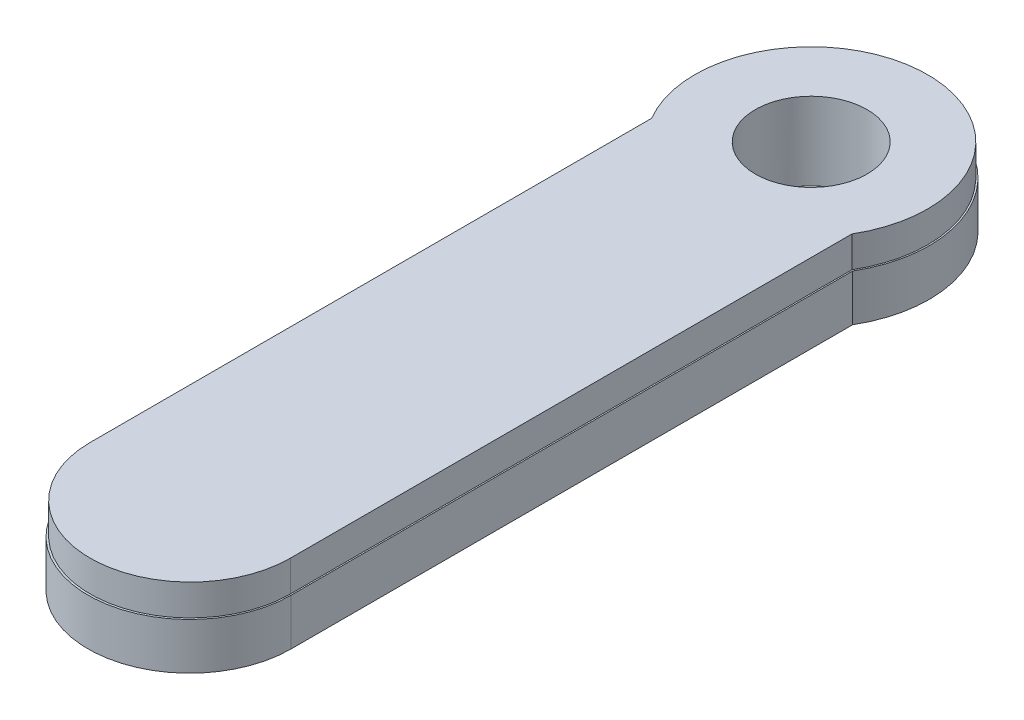
SolidWorks part; units mm, degrees
ref_plane "前基準面" through (0, 0, 0) normal (0, 0, 1) x (1, 0, 0)
ref_plane "上基準面" through (0, 0, 0) normal (0, 1, 0) x (1, 0, 0)
ref_plane "右基準面" through (0, 0, 0) normal (1, 0, 0) x (0, 0, -1)
sketch "草圖1" plane through (0, 0, 0) normal (0, 1, 0) x (1, 0, 0)
  line L0 (-2.6, -2.49) -> (-2.05, -14.6776)
  line L2 (0, -55) -> (0, 55) construction
  line L4 (2.6, -2.49) -> (2.05, -14.6776)
  line L9 (-6.5419, -3.8683) -> (-6.5419, -40.0445)
  line L11 (6.5419, -40.0445) -> (6.5419, -3.8683)
  line L13 (-6.5419, -3.8683) -> (-6.0459, -14.8579) construction
  line L14 (6.5419, -3.8683) -> (6.0459, -14.8579) construction
  arc A0 (2.6, -2.49) -> (-2.6, -2.49) centre (0, 0) ccw
  arc A3 (-2.05, -14.6776) -> (2.05, -14.6776) centre (0, -14.5851) ccw
  arc A7 (6.5419, -3.8683) -> (-6.5419, -3.8683) centre (0, 0) ccw
  arc A8 (-6.5419, -40.0445) -> (6.5419, -40.0445) centre (0, -40.0445) ccw
  arc A9 (-6.0459, -14.8579) -> (6.0459, -14.8579) centre (0, -14.5851) ccw construction
  dimension "D1" = 7.2
  dimension "D2" = 5.2
  dimension "D3" = 12.2
  dimension "D4" = 12.2
  dimension "D5" = 4.1
  dimension "D6" = 2.05
  dimension "D7" = 4
  dimension "D8" = 2.6
extrude "填料-伸長1" add sketch "草圖1" along normal blind 3
sketch "草圖2" plane through (0, 3, 0) normal (0, 1, 0) x (1, 0, 0)
  line L2 (-6.452, -3.8238) -> (-6.452, -40)
  line L3 (6.452, -40) -> (6.452, -3.8238)
  arc A2 (6.452, -3.8238) -> (-6.452, -3.8238) centre (0, 0) ccw
  arc A3 (-6.452, -40) -> (6.452, -40) centre (0, -40) ccw
  circle A4 centre (0, 0) radius 3.6
  dimension "D1" = 7.2
extrude "填料-伸長2" add sketch "草圖2" along normal blind 2
